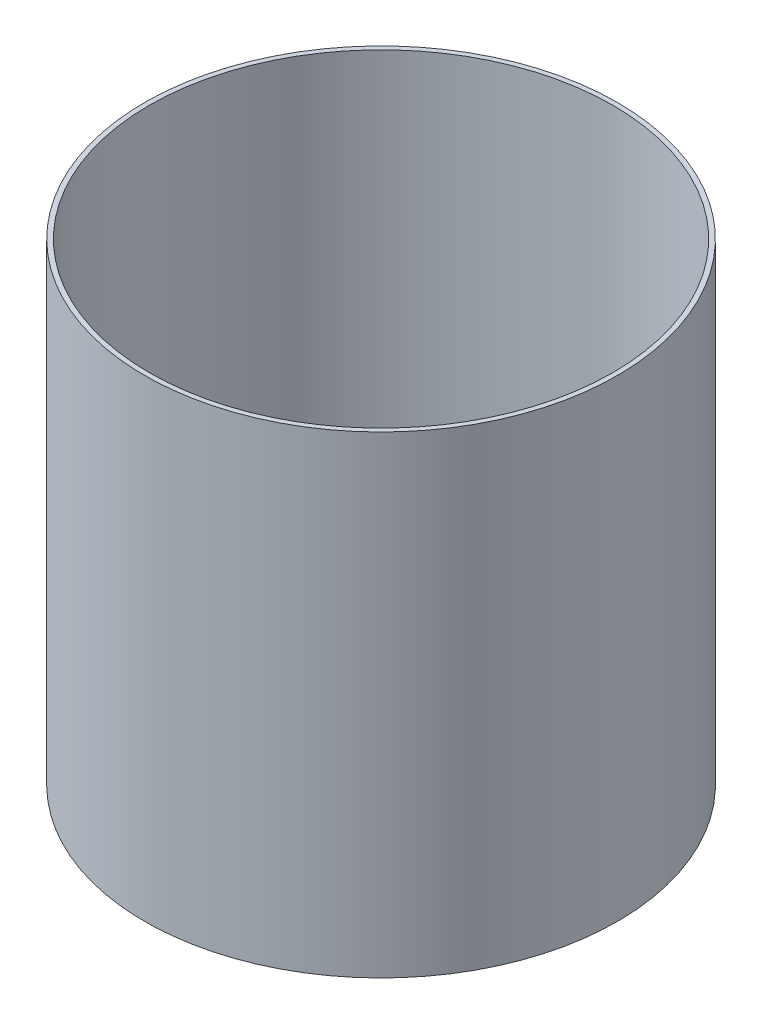
SolidWorks part; units mm, degrees
ref_plane "Alzado" through (0, 0, 0) normal (0, 0, 1) x (1, 0, 0)
ref_plane "Planta" through (0, 0, 0) normal (0, 1, 0) x (1, 0, 0)
ref_plane "Vista lateral" through (0, 0, 0) normal (1, 0, 0) x (0, 0, -1)
sketch "Croquis1" plane through (0, 0, 0) normal (0, 0, 1) x (1, 0, 0)
  line L0 (0, 0) -> (0, 744.5296) construction
  line L1 (-250, 500) -> (0, 500)
  line L2 (-250, 500) -> (-250, 0)
  line L3 (-250, 0) -> (0, 0)
  line L4 (0, 500) -> (0, 0)
  dimension "D1" = 250
  dimension "D2" = 500
revolve "Revolución1" add sketch "Croquis1" angle 360 about L0
shell "Vaciado1" thickness 5
